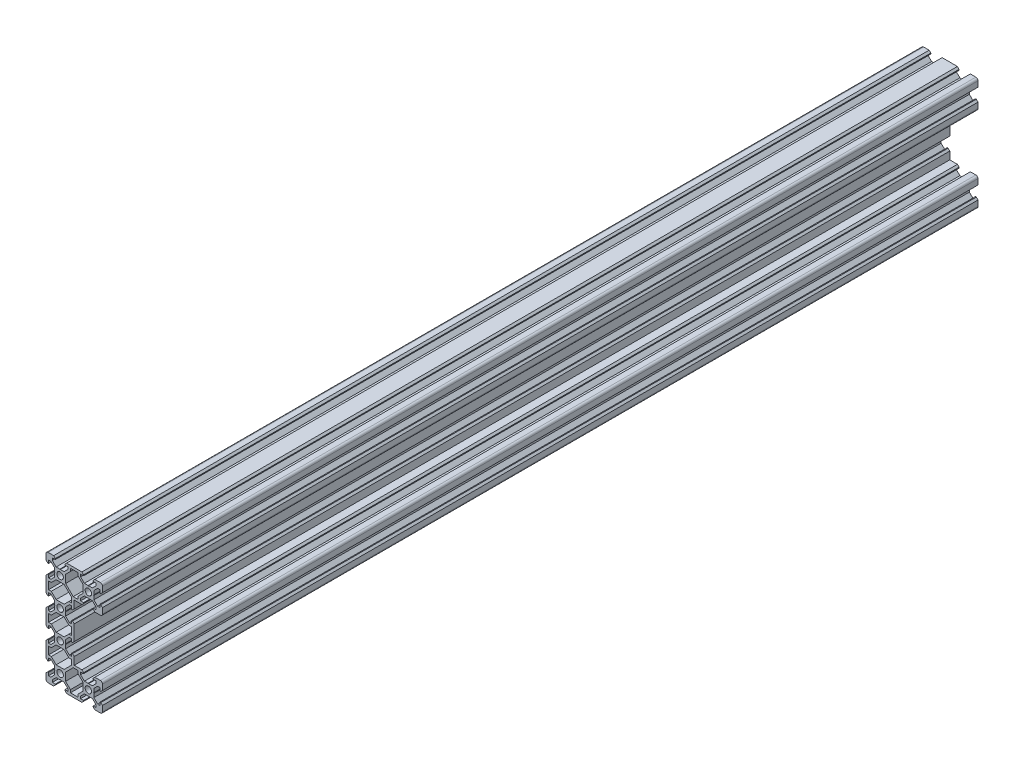
SolidWorks part; units mm, degrees
material "6061-T6 (SS)"
ref_plane "Front Plane" through (0, 0, 0) normal (0, 0, 1) x (1, 0, 0)
ref_plane "Top Plane" through (0, 0, 0) normal (0, 1, 0) x (1, 0, 0)
ref_plane "Right Plane" through (0, 0, 0) normal (1, 0, 0) x (0, 0, -1)
sketch "Sketch1" plane through (0, 0, 0) normal (0, 0, 1) x (1, 0, 0)
  line L0 (-20, -38.5) -> (-20, 38.5)
  line L1 (-18.5, 40) -> (18.5, 40)
  line L2 (20, 38.5) -> (20, 21.5)
  line L3 (18.5, 20) -> (0, 20)
  line L4 (0, 20) -> (0, -20)
  line L5 (0, 0) -> (-20, 0) construction
  line L6 (18.5, -20) -> (0, -20)
  line L7 (20, -38.5) -> (20, -21.5)
  line L8 (-18.5, -40) -> (18.5, -40)
  line L9 (20, 30) -> (10, 30) construction
  line L10 (-10, 0) -> (-10, 10) construction
  arc A0 (-18.5, -40) -> (-20, -38.5) centre (-18.5, -38.5) cw
  arc A1 (20, -38.5) -> (18.5, -40) centre (18.5, -38.5) cw
  arc A2 (18.5, -20) -> (20, -21.5) centre (18.5, -21.5) cw
  arc A3 (20, 21.5) -> (18.5, 20) centre (18.5, 21.5) cw
  arc A4 (18.5, 40) -> (20, 38.5) centre (18.5, 38.5) cw
  arc A5 (-20, 38.5) -> (-18.5, 40) centre (-18.5, 38.5) cw
  circle A6 centre (10, 30) radius 2.3
  circle A7 centre (-10, 30) radius 2.3
  circle A8 centre (-10, 10) radius 2.3
  circle A9 centre (-10, -10) radius 2.3
  circle A10 centre (10, -30) radius 2.3
  circle A11 centre (-10, -30) radius 2.3
  point P13 (-20, -40)
  point P16 (20, -40)
  point P19 (20, -20)
  point P22 (20, 20)
  point P25 (20, 40)
  point P28 (-20, 40)
  line B0 (-10, 30) -> (-10, 40) construction
  line B1 (-10, 33.69) -> (-10.21, 33.9)
  line B2 (-10.21, 33.9) -> (-12.8393, 33.9)
  line B3 (-12.8393, 33.9) -> (-15.5, 36.5607)
  line B4 (-15.5, 36.5607) -> (-15.5, 38.2)
  line B5 (-15.5, 38.2) -> (-13.395, 38.2)
  line B6 (-13.395, 38.2) -> (-13.395, 38.815)
  line B7 (-13.395, 38.815) -> (-14.58, 40)
  line B8 (-14.58, 40) -> (-5.42, 40)
  line B9 (-10, 30) -> (-15.9132, 35.9132) construction
  line B10 (-6.605, 38.815) -> (-5.42, 40)
  line B11 (-6.605, 38.2) -> (-6.605, 38.815)
  line B12 (-4.5, 38.2) -> (-6.605, 38.2)
  line B13 (-4.5, 36.5607) -> (-4.5, 38.2)
  line B14 (-7.1607, 33.9) -> (-4.5, 36.5607)
  line B15 (-9.79, 33.9) -> (-7.1607, 33.9)
  line B16 (-10, 33.69) -> (-9.79, 33.9)
  line B17 (10, 30) -> (10, 40) construction
  line B18 (10, 33.69) -> (9.79, 33.9)
  line B19 (9.79, 33.9) -> (7.1607, 33.9)
  line B20 (7.1607, 33.9) -> (4.5, 36.5607)
  line B21 (4.5, 36.5607) -> (4.5, 38.2)
  line B22 (4.5, 38.2) -> (6.605, 38.2)
  line B23 (6.605, 38.2) -> (6.605, 38.815)
  line B24 (6.605, 38.815) -> (5.42, 40)
  line B25 (5.42, 40) -> (14.58, 40)
  line B26 (10, 30) -> (4.0868, 35.9132) construction
  line B27 (13.395, 38.815) -> (14.58, 40)
  line B28 (13.395, 38.2) -> (13.395, 38.815)
  line B29 (15.5, 38.2) -> (13.395, 38.2)
  line B30 (15.5, 36.5607) -> (15.5, 38.2)
  line B31 (12.8393, 33.9) -> (15.5, 36.5607)
  line B32 (10.21, 33.9) -> (12.8393, 33.9)
  line B33 (10, 33.69) -> (10.21, 33.9)
  line B34 (10, -30) -> (10, -20) construction
  line B35 (10, -26.31) -> (9.79, -26.1)
  line B36 (9.79, -26.1) -> (7.1607, -26.1)
  line B37 (7.1607, -26.1) -> (4.5, -23.4393)
  line B38 (4.5, -23.4393) -> (4.5, -21.8)
  line B39 (4.5, -21.8) -> (6.605, -21.8)
  line B40 (6.605, -21.8) -> (6.605, -21.185)
  line B41 (6.605, -21.185) -> (5.42, -20)
  line B42 (5.42, -20) -> (14.58, -20)
  line B43 (10, -30) -> (4.0868, -24.0868) construction
  line B44 (13.395, -21.185) -> (14.58, -20)
  line B45 (13.395, -21.8) -> (13.395, -21.185)
  line B46 (15.5, -21.8) -> (13.395, -21.8)
  line B47 (15.5, -23.4393) -> (15.5, -21.8)
  line B48 (12.8393, -26.1) -> (15.5, -23.4393)
  line B49 (10.21, -26.1) -> (12.8393, -26.1)
  line B50 (10, -26.31) -> (10.21, -26.1)
  line B51 (-10, 30) -> (-20, 30) construction
  line B52 (-13.69, 30) -> (-13.9, 29.79)
  line B53 (-13.9, 29.79) -> (-13.9, 27.1607)
  line B54 (-13.9, 27.1607) -> (-16.5607, 24.5)
  line B55 (-16.5607, 24.5) -> (-18.2, 24.5)
  line B56 (-18.2, 24.5) -> (-18.2, 26.605)
  line B57 (-18.2, 26.605) -> (-18.815, 26.605)
  line B58 (-18.815, 26.605) -> (-20, 25.42)
  line B59 (-20, 25.42) -> (-20, 34.58)
  line B60 (-10, 30) -> (-15.9132, 24.0868) construction
  line B61 (-18.815, 33.395) -> (-20, 34.58)
  line B62 (-18.2, 33.395) -> (-18.815, 33.395)
  line B63 (-18.2, 35.5) -> (-18.2, 33.395)
  line B64 (-16.5607, 35.5) -> (-18.2, 35.5)
  line B65 (-13.9, 32.8393) -> (-16.5607, 35.5)
  line B66 (-13.9, 30.21) -> (-13.9, 32.8393)
  line B67 (-13.69, 30) -> (-13.9, 30.21)
  line B68 (-10, 10) -> (-20, 10) construction
  line B69 (-13.69, 10) -> (-13.9, 9.79)
  line B70 (-13.9, 9.79) -> (-13.9, 7.1607)
  line B71 (-13.9, 7.1607) -> (-16.5607, 4.5)
  line B72 (-16.5607, 4.5) -> (-18.2, 4.5)
  line B73 (-18.2, 4.5) -> (-18.2, 6.605)
  line B74 (-18.2, 6.605) -> (-18.815, 6.605)
  line B75 (-18.815, 6.605) -> (-20, 5.42)
  line B76 (-20, 5.42) -> (-20, 14.58)
  line B77 (-10, 10) -> (-15.9132, 4.0868) construction
  line B78 (-18.815, 13.395) -> (-20, 14.58)
  line B79 (-18.2, 13.395) -> (-18.815, 13.395)
  line B80 (-18.2, 15.5) -> (-18.2, 13.395)
  line B81 (-16.5607, 15.5) -> (-18.2, 15.5)
  line B82 (-13.9, 12.8393) -> (-16.5607, 15.5)
  line B83 (-13.9, 10.21) -> (-13.9, 12.8393)
  line B84 (-13.69, 10) -> (-13.9, 10.21)
  line B85 (-10, -10) -> (-20, -10) construction
  line B86 (-13.69, -10) -> (-13.9, -10.21)
  line B87 (-13.9, -10.21) -> (-13.9, -12.8393)
  line B88 (-13.9, -12.8393) -> (-16.5607, -15.5)
  line B89 (-16.5607, -15.5) -> (-18.2, -15.5)
  line B90 (-18.2, -15.5) -> (-18.2, -13.395)
  line B91 (-18.2, -13.395) -> (-18.815, -13.395)
  line B92 (-18.815, -13.395) -> (-20, -14.58)
  line B93 (-20, -14.58) -> (-20, -5.42)
  line B94 (-10, -10) -> (-15.9132, -15.9132) construction
  line B95 (-18.815, -6.605) -> (-20, -5.42)
  line B96 (-18.2, -6.605) -> (-18.815, -6.605)
  line B97 (-18.2, -4.5) -> (-18.2, -6.605)
  line B98 (-16.5607, -4.5) -> (-18.2, -4.5)
  line B99 (-13.9, -7.1607) -> (-16.5607, -4.5)
  line B100 (-13.9, -9.79) -> (-13.9, -7.1607)
  line B101 (-13.69, -10) -> (-13.9, -9.79)
  line B102 (-10, -30) -> (-20, -30) construction
  line B103 (-13.69, -30) -> (-13.9, -30.21)
  line B104 (-13.9, -30.21) -> (-13.9, -32.8393)
  line B105 (-13.9, -32.8393) -> (-16.5607, -35.5)
  line B106 (-16.5607, -35.5) -> (-18.2, -35.5)
  line B107 (-18.2, -35.5) -> (-18.2, -33.395)
  line B108 (-18.2, -33.395) -> (-18.815, -33.395)
  line B109 (-18.815, -33.395) -> (-20, -34.58)
  line B110 (-20, -34.58) -> (-20, -25.42)
  line B111 (-10, -30) -> (-15.9132, -35.9132) construction
  line B112 (-18.815, -26.605) -> (-20, -25.42)
  line B113 (-18.2, -26.605) -> (-18.815, -26.605)
  line B114 (-18.2, -24.5) -> (-18.2, -26.605)
  line B115 (-16.5607, -24.5) -> (-18.2, -24.5)
  line B116 (-13.9, -27.1607) -> (-16.5607, -24.5)
  line B117 (-13.9, -29.79) -> (-13.9, -27.1607)
  line B118 (-13.69, -30) -> (-13.9, -29.79)
  line B119 (-10, -30) -> (-10, -40) construction
  line B120 (-10, -33.69) -> (-9.79, -33.9)
  line B121 (-9.79, -33.9) -> (-7.1607, -33.9)
  line B122 (-7.1607, -33.9) -> (-4.5, -36.5607)
  line B123 (-4.5, -36.5607) -> (-4.5, -38.2)
  line B124 (-4.5, -38.2) -> (-6.605, -38.2)
  line B125 (-6.605, -38.2) -> (-6.605, -38.815)
  line B126 (-6.605, -38.815) -> (-5.42, -40)
  line B127 (-5.42, -40) -> (-14.58, -40)
  line B128 (-10, -30) -> (-4.0868, -35.9132) construction
  line B129 (-13.395, -38.815) -> (-14.58, -40)
  line B130 (-13.395, -38.2) -> (-13.395, -38.815)
  line B131 (-15.5, -38.2) -> (-13.395, -38.2)
  line B132 (-15.5, -36.5607) -> (-15.5, -38.2)
  line B133 (-12.8393, -33.9) -> (-15.5, -36.5607)
  line B134 (-10.21, -33.9) -> (-12.8393, -33.9)
  line B135 (-10, -33.69) -> (-10.21, -33.9)
  line B136 (10, -30) -> (10, -40) construction
  line B137 (10, -33.69) -> (10.21, -33.9)
  line B138 (10.21, -33.9) -> (12.8393, -33.9)
  line B139 (12.8393, -33.9) -> (15.5, -36.5607)
  line B140 (15.5, -36.5607) -> (15.5, -38.2)
  line B141 (15.5, -38.2) -> (13.395, -38.2)
  line B142 (13.395, -38.2) -> (13.395, -38.815)
  line B143 (13.395, -38.815) -> (14.58, -40)
  line B144 (14.58, -40) -> (5.42, -40)
  line B145 (10, -30) -> (15.9132, -35.9132) construction
  line B146 (6.605, -38.815) -> (5.42, -40)
  line B147 (6.605, -38.2) -> (6.605, -38.815)
  line B148 (4.5, -38.2) -> (6.605, -38.2)
  line B149 (4.5, -36.5607) -> (4.5, -38.2)
  line B150 (7.1607, -33.9) -> (4.5, -36.5607)
  line B151 (9.79, -33.9) -> (7.1607, -33.9)
  line B152 (10, -33.69) -> (9.79, -33.9)
  line B153 (10, 30) -> (10, 20) construction
  line B154 (10, 26.31) -> (10.21, 26.1)
  line B155 (10.21, 26.1) -> (12.8393, 26.1)
  line B156 (12.8393, 26.1) -> (15.5, 23.4393)
  line B157 (15.5, 23.4393) -> (15.5, 21.8)
  line B158 (15.5, 21.8) -> (13.395, 21.8)
  line B159 (13.395, 21.8) -> (13.395, 21.185)
  line B160 (13.395, 21.185) -> (14.58, 20)
  line B161 (14.58, 20) -> (5.42, 20)
  line B162 (10, 30) -> (15.9132, 24.0868) construction
  line B163 (6.605, 21.185) -> (5.42, 20)
  line B164 (6.605, 21.8) -> (6.605, 21.185)
  line B165 (4.5, 21.8) -> (6.605, 21.8)
  line B166 (4.5, 23.4393) -> (4.5, 21.8)
  line B167 (7.1607, 26.1) -> (4.5, 23.4393)
  line B168 (9.79, 26.1) -> (7.1607, 26.1)
  line B169 (10, 26.31) -> (9.79, 26.1)
  line B170 (-10, 10) -> (0, 10) construction
  line B171 (-6.31, 10) -> (-6.1, 10.21)
  line B172 (-6.1, 10.21) -> (-6.1, 12.8393)
  line B173 (-6.1, 12.8393) -> (-3.4393, 15.5)
  line B174 (-3.4393, 15.5) -> (-1.8, 15.5)
  line B175 (-1.8, 15.5) -> (-1.8, 13.395)
  line B176 (-1.8, 13.395) -> (-1.185, 13.395)
  line B177 (-1.185, 13.395) -> (0, 14.58)
  line B178 (0, 14.58) -> (0, 5.42)
  line B179 (-10, 10) -> (-4.0868, 15.9132) construction
  line B180 (-1.185, 6.605) -> (0, 5.42)
  line B181 (-1.8, 6.605) -> (-1.185, 6.605)
  line B182 (-1.8, 4.5) -> (-1.8, 6.605)
  line B183 (-3.4393, 4.5) -> (-1.8, 4.5)
  line B184 (-6.1, 7.1607) -> (-3.4393, 4.5)
  line B185 (-6.1, 9.79) -> (-6.1, 7.1607)
  line B186 (-6.31, 10) -> (-6.1, 9.79)
  line B187 (-10, -10) -> (0, -10) construction
  line B188 (-6.31, -10) -> (-6.1, -9.79)
  line B189 (-6.1, -9.79) -> (-6.1, -7.1607)
  line B190 (-6.1, -7.1607) -> (-3.4393, -4.5)
  line B191 (-3.4393, -4.5) -> (-1.8, -4.5)
  line B192 (-1.8, -4.5) -> (-1.8, -6.605)
  line B193 (-1.8, -6.605) -> (-1.185, -6.605)
  line B194 (-1.185, -6.605) -> (0, -5.42)
  line B195 (0, -5.42) -> (0, -14.58)
  line B196 (-10, -10) -> (-4.0868, -4.0868) construction
  line B197 (-1.185, -13.395) -> (0, -14.58)
  line B198 (-1.8, -13.395) -> (-1.185, -13.395)
  line B199 (-1.8, -15.5) -> (-1.8, -13.395)
  line B200 (-3.4393, -15.5) -> (-1.8, -15.5)
  line B201 (-6.1, -12.8393) -> (-3.4393, -15.5)
  line B202 (-6.1, -10.21) -> (-6.1, -12.8393)
  line B203 (-6.31, -10) -> (-6.1, -10.21)
  line B204 (10, -30) -> (20, -30) construction
  line B205 (13.69, -30) -> (13.9, -29.79)
  line B206 (13.9, -29.79) -> (13.9, -27.1607)
  line B207 (13.9, -27.1607) -> (16.5607, -24.5)
  line B208 (16.5607, -24.5) -> (18.2, -24.5)
  line B209 (18.2, -24.5) -> (18.2, -26.605)
  line B210 (18.2, -26.605) -> (18.815, -26.605)
  line B211 (18.815, -26.605) -> (20, -25.42)
  line B212 (20, -25.42) -> (20, -34.58)
  line B213 (10, -30) -> (15.9132, -24.0868) construction
  line B214 (18.815, -33.395) -> (20, -34.58)
  line B215 (18.2, -33.395) -> (18.815, -33.395)
  line B216 (18.2, -35.5) -> (18.2, -33.395)
  line B217 (16.5607, -35.5) -> (18.2, -35.5)
  line B218 (13.9, -32.8393) -> (16.5607, -35.5)
  line B219 (13.9, -30.21) -> (13.9, -32.8393)
  line B220 (13.69, -30) -> (13.9, -30.21)
  line B221 (10, 30) -> (20, 30) construction
  line B222 (13.69, 30) -> (13.9, 30.21)
  line B223 (13.9, 30.21) -> (13.9, 32.8393)
  line B224 (13.9, 32.8393) -> (16.5607, 35.5)
  line B225 (16.5607, 35.5) -> (18.2, 35.5)
  line B226 (18.2, 35.5) -> (18.2, 33.395)
  line B227 (18.2, 33.395) -> (18.815, 33.395)
  line B228 (18.815, 33.395) -> (20, 34.58)
  line B229 (20, 34.58) -> (20, 25.42)
  line B230 (10, 30) -> (15.9132, 35.9132) construction
  line B231 (18.815, 26.605) -> (20, 25.42)
  line B232 (18.2, 26.605) -> (18.815, 26.605)
  line B233 (18.2, 24.5) -> (18.2, 26.605)
  line B234 (16.5607, 24.5) -> (18.2, 24.5)
  line B235 (13.9, 27.1607) -> (16.5607, 24.5)
  line B236 (13.9, 29.79) -> (13.9, 27.1607)
  line B237 (13.69, 30) -> (13.9, 29.79)
  line B238 (-18.2, -2.7) -> (-18.2, 2.7)
  line B239 (-18.2, 2.7) -> (-16.2393, 2.7)
  line B240 (-16.2393, 2.7) -> (-12.8393, 6.1)
  line B241 (-12.8393, 6.1) -> (-7.1607, 6.1)
  line B242 (-10, 6.1) -> (-10, 0) construction
  line B243 (-10, 0) -> (-18.2, 0) construction
  line B244 (-3.7607, 2.7) -> (-7.1607, 6.1)
  line B245 (-1.8, 2.7) -> (-3.7607, 2.7)
  line B246 (-1.8, -2.7) -> (-1.8, 2.7)
  line B247 (-1.8, -2.7) -> (-3.7607, -2.7)
  line B248 (-3.7607, -2.7) -> (-7.1607, -6.1)
  line B249 (-12.8393, -6.1) -> (-7.1607, -6.1)
  line B250 (-16.2393, -2.7) -> (-12.8393, -6.1)
  line B251 (-18.2, -2.7) -> (-16.2393, -2.7)
  line B252 (-10, 6.1) -> (-10, 10) construction
  line B253 (-10, 10) -> (-15.0927, 4.9073) construction
  line B254 (-18.2, 17.3) -> (-18.2, 22.7)
  line B255 (-18.2, 22.7) -> (-16.2393, 22.7)
  line B256 (-16.2393, 22.7) -> (-12.8393, 26.1)
  line B257 (-12.8393, 26.1) -> (-7.1607, 26.1)
  line B258 (-10, 26.1) -> (-10, 20) construction
  line B259 (-10, 20) -> (-18.2, 20) construction
  line B260 (-1.8, 17.3) -> (-3.7607, 17.3)
  line B261 (-3.7607, 17.3) -> (-7.1607, 13.9)
  line B262 (-12.8393, 13.9) -> (-7.1607, 13.9)
  line B263 (-16.2393, 17.3) -> (-12.8393, 13.9)
  line B264 (-18.2, 17.3) -> (-16.2393, 17.3)
  line B265 (-10, 26.1) -> (-10, 30) construction
  line B266 (-10, 30) -> (-15.0927, 24.9073) construction
  line B267 (-7.1607, 26.1) -> (-1.8, 20.7393)
  line B268 (-1.8, 17.3) -> (-1.8, 20.7393)
  line B269 (2.7, -38.2) -> (-2.7, -38.2)
  line B270 (-2.7, -38.2) -> (-2.7, -36.2393)
  line B271 (-2.7, -36.2393) -> (-6.1, -32.8393)
  line B272 (-6.1, -32.8393) -> (-6.1, -27.1607)
  line B273 (-6.1, -30) -> (0, -30) construction
  line B274 (0, -30) -> (0, -38.2) construction
  line B275 (2.7, -21.8) -> (2.7, -23.7607)
  line B276 (2.7, -23.7607) -> (6.1, -27.1607)
  line B277 (6.1, -32.8393) -> (6.1, -27.1607)
  line B278 (2.7, -36.2393) -> (6.1, -32.8393)
  line B279 (2.7, -38.2) -> (2.7, -36.2393)
  line B280 (-6.1, -30) -> (-10, -30) construction
  line B281 (-10, -30) -> (-4.9073, -35.0927) construction
  line B282 (-6.1, -27.1607) -> (-0.7393, -21.8)
  line B283 (2.7, -21.8) -> (-0.7393, -21.8)
  line B284 (-18.2, -22.7) -> (-18.2, -17.3)
  line B285 (-18.2, -17.3) -> (-16.2393, -17.3)
  line B286 (-16.2393, -17.3) -> (-12.8393, -13.9)
  line B287 (-12.8393, -13.9) -> (-7.1607, -13.9)
  line B288 (-10, -13.9) -> (-10, -20) construction
  line B289 (-10, -20) -> (-18.2, -20) construction
  line B290 (-12.8393, -26.1) -> (-7.1607, -26.1)
  line B291 (-16.2393, -22.7) -> (-12.8393, -26.1)
  line B292 (-18.2, -22.7) -> (-16.2393, -22.7)
  line B293 (-10, -13.9) -> (-10, -10) construction
  line B294 (-10, -10) -> (-15.0927, -15.0927) construction
  line B295 (-3.7607, -17.3) -> (-7.1607, -13.9)
  line B296 (-1.8, -17.3) -> (-3.7607, -17.3)
  line B297 (-1.8, -17.3) -> (-1.8, -20.7393)
  line B298 (-1.8, -20.7393) -> (-7.1607, -26.1)
  line B299 (-2.7, 38.2) -> (2.7, 38.2)
  line B300 (2.7, 38.2) -> (2.7, 36.2393)
  line B301 (2.7, 36.2393) -> (6.1, 32.8393)
  line B302 (6.1, 32.8393) -> (6.1, 27.1607)
  line B303 (6.1, 30) -> (0, 30) construction
  line B304 (0, 30) -> (0, 38.2) construction
  line B305 (-6.1, 32.8393) -> (-6.1, 27.1607)
  line B306 (-2.7, 36.2393) -> (-6.1, 32.8393)
  line B307 (-2.7, 38.2) -> (-2.7, 36.2393)
  line B308 (6.1, 30) -> (10, 30) construction
  line B309 (10, 30) -> (4.9073, 35.0927) construction
  line B310 (2.7, 23.7607) -> (6.1, 27.1607)
  line B311 (2.7, 21.8) -> (2.7, 23.7607)
  line B312 (2.7, 21.8) -> (-0.7393, 21.8)
  line B313 (-0.7393, 21.8) -> (-6.1, 27.1607)
  dimension "D3" = 1.5
  dimension "D6" = 4.6
  dimension "D7" = 20
  dimension "D8" = 20
  dimension "D1" = 40
  dimension "D2" = 80
  dimension "D4" = 20
  dimension "D5" = 20
sketch_block_instance "V Slot 2-1"
sketch_block "V Slot 2" parameters "D1"=10, "D2"=11, "D3"=4.3, "D4"=1.8, "D5"=0.21, "D6"=45, "D7"=9.16, "D8"=1.5, "D9"=6.79
sketch_block_instance "V Slot 2-2"
sketch_block_instance "V Slot 2-3"
sketch_block_instance "V Slot 2-4"
sketch_block_instance "V Slot 2-5"
sketch_block_instance "V Slot 2-6"
sketch_block_instance "V Slot 2-7"
sketch_block_instance "V Slot 2-8"
sketch_block_instance "V Slot 2-9"
sketch_block_instance "V Slot 2-10"
sketch_block_instance "V Slot 2-11"
sketch_block_instance "V Slot 2-12"
sketch_block_instance "V Slot 2-13"
sketch_block_instance "V Slot 2-14"
sketch_block_instance "Center Cutout 1-1"
sketch_block "Center Cutout 1" parameters "D1"=5.4, "D2"=12.2, "D3"=8.2, "D4"=45, "D5"=10, "D6"=1.5
sketch_block_instance "Corner Cutout 1-1"
sketch_block "Corner Cutout 1" parameters "D1"=5.4, "D2"=12.2, "D3"=8.2, "D4"=45, "D5"=10, "D6"=1.5
sketch_block_instance "Corner Cutout 1-2"
sketch_block_instance "Corner Cutout 2-1"
sketch_block "Corner Cutout 2" parameters "D1"=5.4, "D2"=12.2, "D3"=8.2, "D4"=45, "D5"=10, "D6"=1.5
sketch_block_instance "Corner Cutout 2-2"
extrude "Boss-Extrude1" add sketch "Sketch1" along normal blind 620 contours B237 B222 B223 B224 B225 B226 B227 B228 L2 A4 L1 B27 B28 B29 B30 B31 B32 B33 B18 B19 B20 B21 B22 B23 B24 B10 B11 B12 B13 B14 B15 B16 B1 B2 B3 B4 B5 B6 B7 A5 L0 B61 B62 B63 B64 B65 B66 B67 B52
